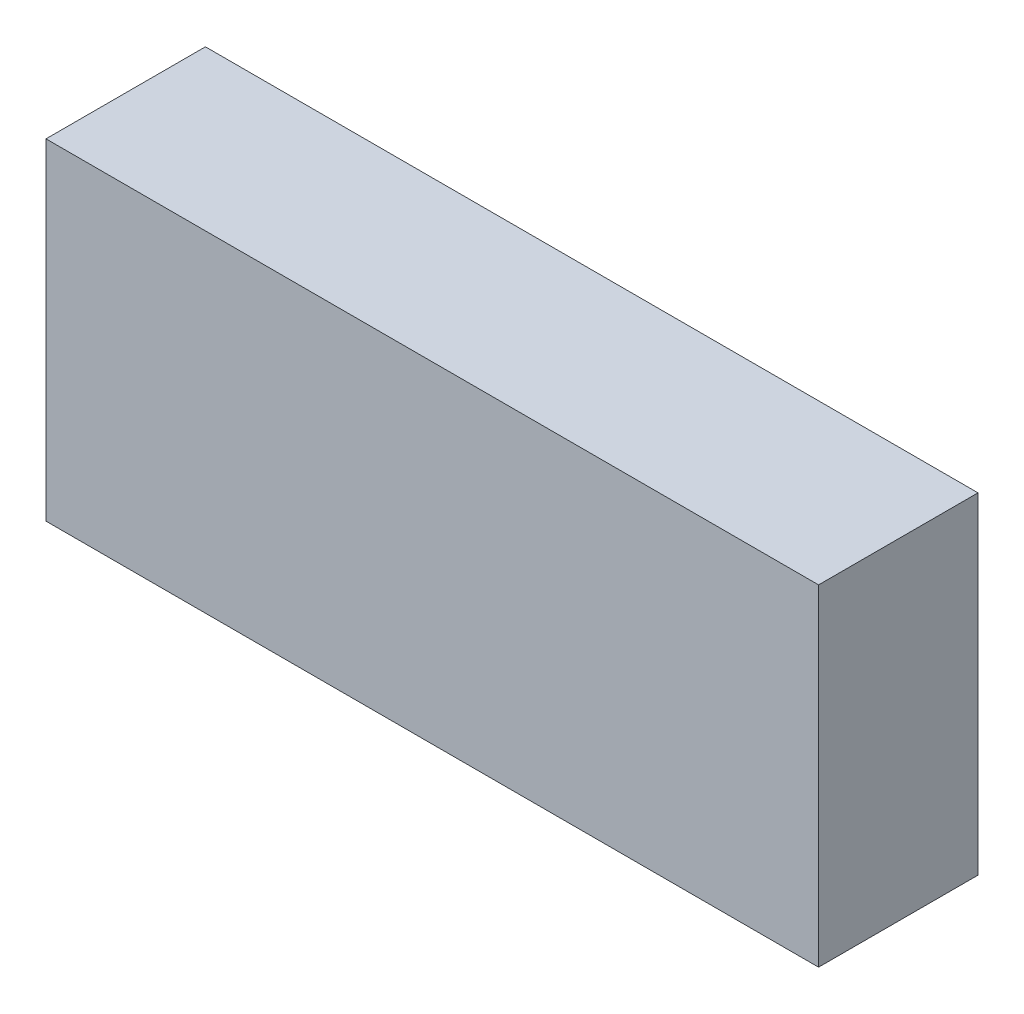
SolidWorks part; units mm, degrees
ref_plane "前视基准面" through (0, 0, 0) normal (0, 0, 1) x (1, 0, 0)
ref_plane "上视基准面" through (0, 0, 0) normal (0, 1, 0) x (1, 0, 0)
ref_plane "右视基准面" through (0, 0, 0) normal (1, 0, 0) x (0, 0, -1)
sketch "草图1" plane through (0, 0, 0) normal (0, 0, 1) x (1, 0, 0)
  line L1 (-31.5, 13.5) -> (31.5, 13.5)
  line L2 (-31.5, 13.5) -> (-31.5, -13.5)
  line L3 (-31.5, -13.5) -> (31.5, -13.5)
  line L4 (31.5, 13.5) -> (31.5, -13.5)
  line L5 (0, -13.5) -> (0, 13.5) construction
  line L6 (-31.5, 0) -> (31.5, 0) construction
  point P0 (0, 0)
  dimension "D1" = 63
  dimension "D2" = 27
extrude "凸台-拉伸1" add sketch "草图1" along normal blind 13
